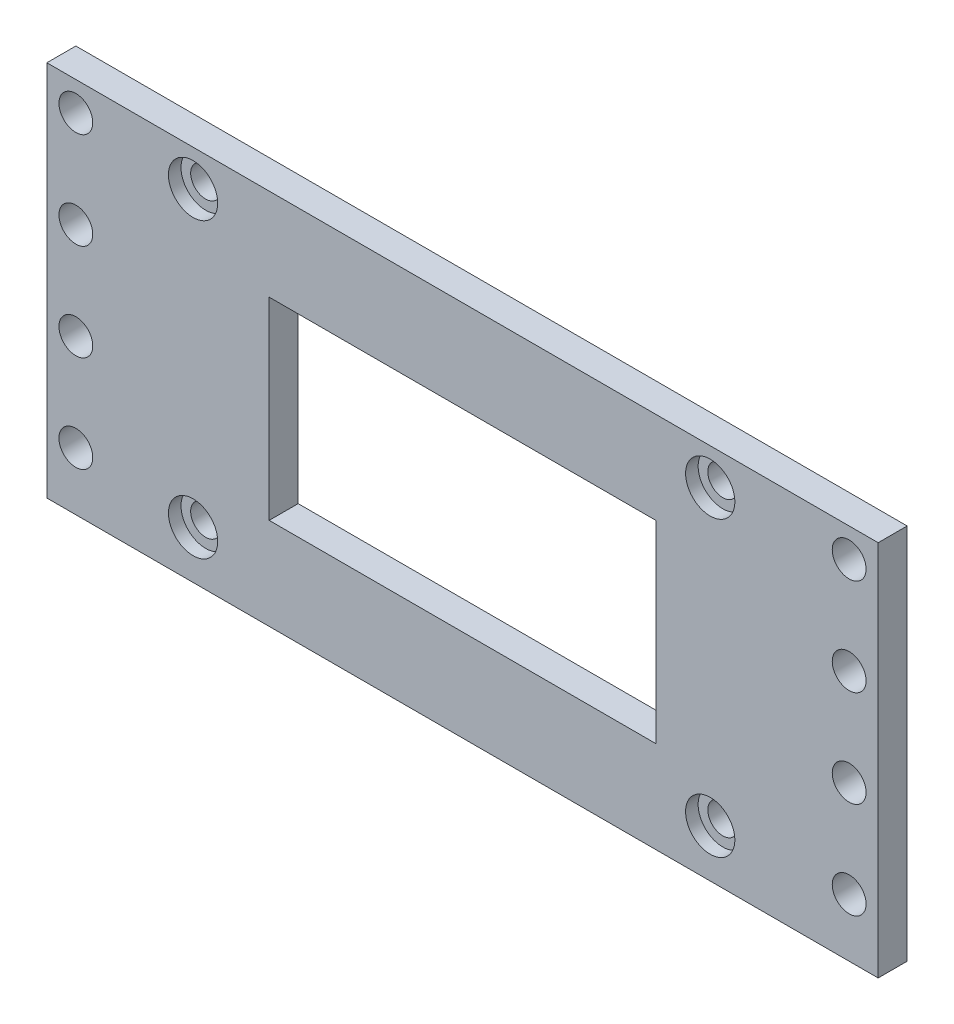
SolidWorks part; units mm, degrees
ref_plane "Front Plane" through (0, 0, 0) normal (0, 0, 1) x (1, 0, 0)
ref_plane "Top Plane" through (0, 0, 0) normal (0, 1, 0) x (1, 0, 0)
ref_plane "Right Plane" through (0, 0, 0) normal (1, 0, 0) x (0, 0, -1)
sketch "Sketch1" plane through (0, 0, 0) normal (0, 0, 1) x (1, 0, 0)
  line L0 (0, 24.6211) -> (0, 20.3728) construction
  line L1 (-31, -19) -> (31, -19)
  line L2 (-31, -19) -> (-31, 19)
  line L3 (-31, 19) -> (31, 19)
  line L4 (31, -19) -> (31, 19)
  line L5 (-31, -19) -> (31, 19) construction
  line L6 (-31, 19) -> (31, -19) construction
  line L7 (-49.6059, 0) -> (-34.1469, 0) construction
  line L9 (-20, -10) -> (20, -10)
  line L10 (-20, -10) -> (-20, 10)
  line L11 (-20, 10) -> (20, 10)
  line L12 (20, -10) -> (20, 10)
  line L13 (-20, -10) -> (20, 10) construction
  line L14 (-20, 10) -> (20, -10) construction
  circle A0 centre (-27.8731, 15.75) radius 1.55
  circle A1 centre (25.6269, 15.75) radius 1.55
  circle A2 centre (-27.8731, -14.55) radius 1.55
  circle A3 centre (25.6269, -14.55) radius 1.55
  point P0 (0, 0)
  point P12 (-31, 0)
  point P13 (0, 19)
  point P20 (0, 0)
  point P25 (0, 0)
  point P26 (0, 0)
  point P27 (0, 0)
  point P28 (0, 0)
  point P29 (0, 0)
  point P30 (0, 0)
  dimension "D5" = 3.1
  dimension "D1" = 62
  dimension "D2" = 38
  dimension "D3" = 4.51
  dimension "D4" = 3.25
  dimension "D6" = 53.5
  dimension "D7" = 30.3
  dimension "D8" = 20
  dimension "D9" = 40
extrude "Boss-Extrude1" add sketch "Sketch1" along normal blind 3
sketch "Sketch3" plane through (0, 0, 3) normal (0, 0, 1) x (1, 0, 0)
  line L8 (31, -19) -> (31, 19)
  line L9 (-31, -19) -> (31, -19)
  line L10 (-31, 19) -> (-31, -19)
  line L11 (31, 19) -> (-31, 19)
  line L12 (43, -19.5) -> (43, 19.5)
  line L13 (43, 19.5) -> (-43, 19.5)
  line L14 (-43, 19.5) -> (-43, -19.5)
  line L15 (-43, -19.5) -> (43, -19.5)
  line L16 (31, -19) -> (31, 19)
  line L17 (-31, -19) -> (31, -19)
  line L18 (-31, 19) -> (-31, -19)
  line L19 (31, 19) -> (-31, 19)
  point P3 (0, 0)
  point P4 (0, 19.5)
  point P9 (0, 19)
  point P11 (-43, 0)
  point P12 (-31, 0)
  dimension "D1" = 0
  dimension "D2" = 86
  dimension "D3" = 39
extrude "Boss-Extrude2" add sketch "Sketch3" against normal up to surface (3 mm away) up to face at (-29.4231, -14.55, 0)
sketch "Sketch4" plane through (0, 0, 0) normal (0, 0, -1) x (-1, 0, 0)
  line L0 (-43, 19.5) -> (43, 19.5) construction
  line L1 (-43, -19.5) -> (-43, 19.5) construction
  circle A0 centre (-40, 16.5) radius 1.75
  point P2 (0, 0)
  point P7 (0, 0)
  dimension "D1" = 3.5
  dimension "D2" = 3
  dimension "D3" = 3
extrude "Cut-Extrude1" cut sketch "Sketch4" against normal blind 3
sketch "Sketch5" plane through (0, 0, 3) normal (0, 0, 1) x (1, 0, 0)
  circle A0 centre (-27.8731, 15.75) radius 2.55
  circle A1 centre (-27.8731, -14.55) radius 2.55
  circle A2 centre (25.6269, -14.55) radius 2.55
  circle A3 centre (25.6269, 15.75) radius 2.55
  circle A4 centre (-27.8731, 15.75) radius 1.55 construction
  circle A5 centre (-27.8731, -14.55) radius 1.55 construction
  circle A6 centre (25.6269, -14.55) radius 1.55 construction
  circle A7 centre (25.6269, 15.75) radius 1.55 construction
  point P8 (0, 0)
  dimension "D1" = 5.1
extrude "Cut-Extrude2" cut sketch "Sketch5" against normal blind 1.3
pattern_linear "LPattern2" count 4 spacing 10 along (0, -1, 0) count 9 spacing 10 along (-1, 0, 0) skipping (0, 1), (0, 2), (0, 3), (0, 4), (0, 5), (0, 6), (0, 7), (1, 1), (1, 2), (1, 3), (1, 4), (1, 5), (1, 6), (1, 7), (2, 1), (2, 2), (2, 3), (2, 4), (2, 5), (2, 6), (2, 7), (3, 1), (3, 2), (3, 3), (3, 4), (3, 5), (3, 6), (3, 7) of "Cut-Extrude1"
